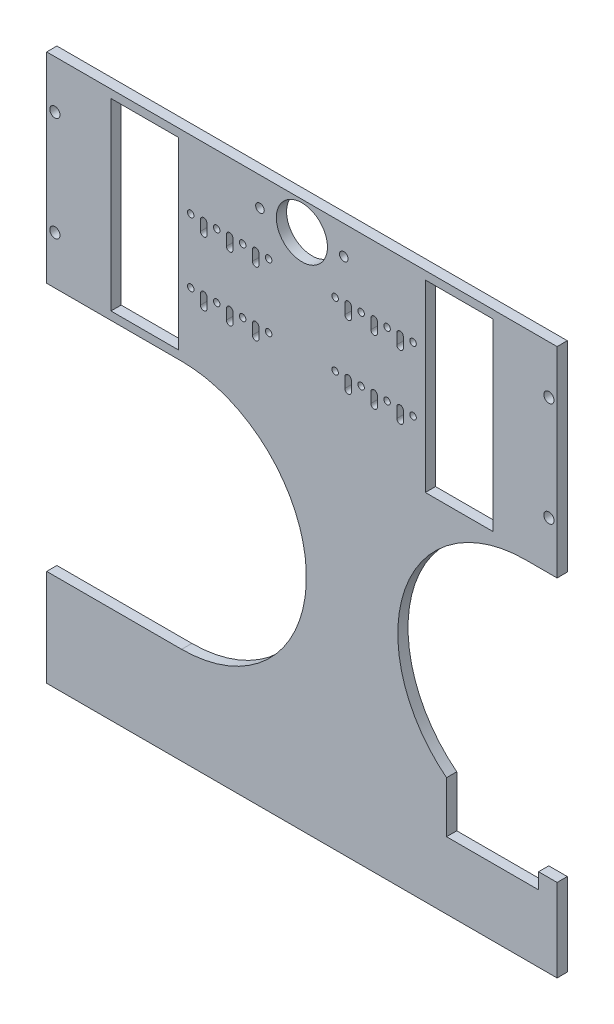
SolidWorks part; units mm, degrees
ref_plane "Front Plane" through (0, 0, 0) normal (0, 0, 1) x (1, 0, 0)
ref_plane "Top Plane" through (0, 0, 0) normal (0, 1, 0) x (1, 0, 0)
ref_plane "Right Plane" through (0, 0, 0) normal (1, 0, 0) x (0, 0, -1)
sketch "Sketch1" plane through (0, 0, 0) normal (0, 0, 1) x (1, 0, 0)
  line L0 (124.8, 0) -> (124.8, -350.4) construction
  line L1 (0, 0) -> (249.6, 0)
  line L2 (0, 0) -> (0, -350.4)
  line L3 (0, -350.4) -> (249.6, -350.4)
  line L4 (249.6, 0) -> (249.6, -350.4)
  line L9 (185.16, -4) -> (218.16, -4)
  line L10 (185.16, -4) -> (185.16, -94)
  line L11 (185.16, -94) -> (218.16, -94)
  line L12 (218.16, -4) -> (218.16, -94)
  line L13 (179.16, -49) -> (228.95, -49) construction
  line L14 (141.06, -33.375) -> (147.41, -33.375) construction
  line L15 (145.3, -14) -> (104.3, -14) construction
  line L21 (179.16, -49) -> (218.16, -49) construction
  line L25 (141.06, -64.625) -> (147.41, -64.625) construction
  line L32 (147.41, -33.375) -> (147.41, -38.375) construction
  line L33 (145.8225, -33.375) -> (145.8225, -38.375)
  line L34 (148.9975, -33.375) -> (148.9975, -38.375)
  line L35 (160.11, -33.375) -> (160.11, -38.375) construction
  line L36 (158.52, -33.375) -> (158.52, -38.375)
  line L37 (161.7, -33.375) -> (161.7, -38.375)
  line L38 (172.81, -33.375) -> (172.81, -38.375) construction
  line L39 (171.22, -33.375) -> (171.22, -38.375)
  line L40 (174.4, -33.375) -> (174.4, -38.375)
  line L41 (147.41, -33.375) -> (153.76, -33.375) construction
  line L42 (153.76, -33.375) -> (160.11, -33.375) construction
  line L43 (160.11, -33.375) -> (166.46, -33.375) construction
  line L44 (166.46, -33.375) -> (172.81, -33.375) construction
  line L45 (172.81, -33.375) -> (179.16, -33.375) construction
  line L48 (228.95, -49) -> (147.41, -49) construction
  line L52 (204.16, -4) -> (204.16, -94) construction
  line L53 (194.16, -4) -> (214.16, -4) construction
  line L54 (194.16, -4) -> (194.16, -94) construction
  line L55 (194.16, -94) -> (214.16, -94) construction
  line L56 (214.16, -4) -> (214.16, -94) construction
  line L62 (147.41, -64.625) -> (147.41, -69.625) construction
  line L65 (145.8225, -64.625) -> (145.8225, -69.625)
  line L68 (148.9975, -64.625) -> (148.9975, -69.625)
  line L71 (160.11, -64.625) -> (160.11, -69.625) construction
  line L78 (158.52, -64.625) -> (158.52, -69.625)
  line L79 (161.7, -64.625) -> (161.7, -69.625)
  line L80 (172.81, -64.625) -> (172.81, -69.625) construction
  line L83 (171.22, -64.625) -> (171.22, -69.625)
  line L87 (147.41, -49) -> (102.19, -49) construction
  line L90 (179.16, -33.375) -> (179.16, -64.625) construction
  line L93 (147.41, -33.375) -> (147.41, -49) construction
  line L102 (245.6, -23.5) -> (245.6, -74.5) construction
  line L103 (218.16, -49) -> (245.6, -49) construction
  line L105 (174.4, -64.625) -> (174.4, -69.625)
  line L106 (147.41, -64.625) -> (153.76, -64.625) construction
  line L107 (153.76, -64.625) -> (160.11, -64.625) construction
  line L108 (160.11, -64.625) -> (166.46, -64.625) construction
  line L109 (166.46, -64.625) -> (172.81, -64.625) construction
  line L110 (172.81, -64.625) -> (179.16, -64.625) construction
  line L111 (102.19, -33.375) -> (102.19, -38.375) construction
  line L112 (103.7775, -33.375) -> (103.7775, -38.375)
  line L113 (100.6025, -33.375) -> (100.6025, -38.375)
  line L114 (89.49, -33.375) -> (89.49, -38.375) construction
  line L115 (91.08, -33.375) -> (91.08, -38.375)
  line L116 (87.9, -33.375) -> (87.9, -38.375)
  line L117 (76.79, -33.375) -> (76.79, -38.375) construction
  line L118 (78.38, -33.375) -> (78.38, -38.375)
  line L119 (75.2, -33.375) -> (75.2, -38.375)
  line L120 (102.19, -64.625) -> (102.19, -69.625) construction
  line L121 (103.7775, -64.625) -> (103.7775, -69.625)
  line L122 (100.6025, -64.625) -> (100.6025, -69.625)
  line L123 (89.49, -64.625) -> (89.49, -69.625) construction
  line L124 (91.08, -64.625) -> (91.08, -69.625)
  line L125 (87.9, -64.625) -> (87.9, -69.625)
  line L126 (76.79, -64.625) -> (76.79, -69.625) construction
  line L127 (78.38, -64.625) -> (78.38, -69.625)
  line L128 (75.2, -64.625) -> (75.2, -69.625)
  line L129 (76.79, -64.625) -> (70.44, -64.625) construction
  line L130 (83.14, -64.625) -> (76.79, -64.625) construction
  line L131 (89.49, -64.625) -> (83.14, -64.625) construction
  line L132 (95.84, -64.625) -> (89.49, -64.625) construction
  line L133 (102.19, -64.625) -> (95.84, -64.625) construction
  line L134 (31.44, -49) -> (4, -49) construction
  line L135 (4, -23.5) -> (4, -74.5) construction
  line L136 (102.19, -33.375) -> (102.19, -49) construction
  line L137 (70.44, -33.375) -> (70.44, -64.625) construction
  line L139 (35.44, -4) -> (35.44, -94) construction
  line L140 (55.44, -94) -> (35.44, -94) construction
  line L141 (55.44, -4) -> (55.44, -94) construction
  line L142 (55.44, -4) -> (35.44, -4) construction
  line L143 (45.44, -4) -> (45.44, -94) construction
  line L144 (20.65, -49) -> (102.19, -49) construction
  line L145 (76.79, -33.375) -> (70.44, -33.375) construction
  line L146 (83.14, -33.375) -> (76.79, -33.375) construction
  line L147 (89.49, -33.375) -> (83.14, -33.375) construction
  line L148 (95.84, -33.375) -> (89.49, -33.375) construction
  line L149 (102.19, -33.375) -> (95.84, -33.375) construction
  line L150 (108.54, -64.625) -> (102.19, -64.625) construction
  line L151 (70.44, -49) -> (31.44, -49) construction
  line L152 (108.54, -33.375) -> (102.19, -33.375) construction
  line L153 (70.44, -49) -> (20.65, -49) construction
  line L154 (31.44, -4) -> (31.44, -94)
  line L155 (64.44, -94) -> (31.44, -94)
  line L156 (64.44, -4) -> (64.44, -94)
  line L157 (64.44, -4) -> (31.44, -4)
  arc A6 (174.4, -33.375) -> (171.22, -33.375) centre (172.81, -33.375) cw construction
  arc A7 (171.22, -33.375) -> (174.4, -33.375) centre (172.81, -33.375) cw
  arc A10 (158.52, -33.375) -> (161.7, -33.375) centre (160.11, -33.375) cw
  arc A11 (161.7, -33.375) -> (158.52, -33.375) centre (160.11, -33.375) cw construction
  arc A14 (145.8225, -33.375) -> (148.9975, -33.375) centre (147.41, -33.375) cw
  arc A15 (148.9975, -33.375) -> (145.8225, -33.375) centre (147.41, -33.375) cw construction
  circle A38 centre (104.3, -14) radius 2.1
  arc A39 (148.9975, -38.375) -> (145.8225, -38.375) centre (147.41, -38.375) cw
  arc A41 (161.7, -38.375) -> (158.52, -38.375) centre (160.11, -38.375) cw
  arc A43 (174.4, -38.375) -> (171.22, -38.375) centre (172.81, -38.375) cw
  circle A84 centre (245.6, -23.5) radius 2.5
  circle A85 centre (245.6, -74.5) radius 2.5
  circle A109 centre (145.3, -14) radius 2.1
  circle A179 centre (179.16, -33.375) radius 1.59
  arc A182 (174.4, -64.625) -> (171.22, -64.625) centre (172.81, -64.625) cw construction
  arc A183 (171.22, -64.625) -> (174.4, -64.625) centre (172.81, -64.625) cw
  arc A184 (158.52, -64.625) -> (161.7, -64.625) centre (160.11, -64.625) cw
  arc A185 (161.7, -64.625) -> (158.52, -64.625) centre (160.11, -64.625) cw construction
  arc A188 (145.8225, -64.625) -> (148.9975, -64.625) centre (147.41, -64.625) cw
  arc A189 (148.9975, -64.625) -> (145.8225, -64.625) centre (147.41, -64.625) cw construction
  arc A193 (148.9975, -69.625) -> (145.8225, -69.625) centre (147.41, -69.625) cw
  arc A195 (161.7, -69.625) -> (158.52, -69.625) centre (160.11, -69.625) cw
  arc A197 (174.4, -69.625) -> (171.22, -69.625) centre (172.81, -69.625) cw
  circle A198 centre (179.16, -64.625) radius 1.59
  circle A199 centre (124.8, -14) radius 12.5
  circle A200 centre (141.06, -33.375) radius 1.59
  circle A201 centre (153.76, -33.375) radius 1.59
  circle A202 centre (166.46, -33.375) radius 1.59
  circle A203 centre (141.06, -64.625) radius 1.59
  circle A204 centre (153.76, -64.625) radius 1.59
  circle A205 centre (166.46, -64.625) radius 1.59
  arc A206 (103.7775, -33.375) -> (100.6025, -33.375) centre (102.19, -33.375) ccw
  arc A207 (100.6025, -38.375) -> (103.7775, -38.375) centre (102.19, -38.375) ccw
  arc A208 (91.08, -33.375) -> (87.9, -33.375) centre (89.49, -33.375) ccw
  arc A209 (87.9, -38.375) -> (91.08, -38.375) centre (89.49, -38.375) ccw
  arc A210 (78.38, -33.375) -> (75.2, -33.375) centre (76.79, -33.375) ccw
  arc A211 (75.2, -38.375) -> (78.38, -38.375) centre (76.79, -38.375) ccw
  arc A212 (103.7775, -64.625) -> (100.6025, -64.625) centre (102.19, -64.625) ccw
  arc A213 (100.6025, -69.625) -> (103.7775, -69.625) centre (102.19, -69.625) ccw
  arc A214 (91.08, -64.625) -> (87.9, -64.625) centre (89.49, -64.625) ccw
  arc A215 (87.9, -69.625) -> (91.08, -69.625) centre (89.49, -69.625) ccw
  arc A216 (78.38, -64.625) -> (75.2, -64.625) centre (76.79, -64.625) ccw
  arc A217 (75.2, -69.625) -> (78.38, -69.625) centre (76.79, -69.625) ccw
  arc A218 (100.6025, -64.625) -> (103.7775, -64.625) centre (102.19, -64.625) ccw construction
  arc A219 (87.9, -64.625) -> (91.08, -64.625) centre (89.49, -64.625) ccw construction
  arc A220 (75.2, -64.625) -> (78.38, -64.625) centre (76.79, -64.625) ccw construction
  arc A221 (100.6025, -33.375) -> (103.7775, -33.375) centre (102.19, -33.375) ccw construction
  arc A222 (87.9, -33.375) -> (91.08, -33.375) centre (89.49, -33.375) ccw construction
  arc A223 (75.2, -33.375) -> (78.38, -33.375) centre (76.79, -33.375) ccw construction
  circle A224 centre (83.14, -64.625) radius 1.59
  circle A225 centre (95.84, -64.625) radius 1.59
  circle A226 centre (108.54, -64.625) radius 1.59
  circle A227 centre (83.14, -33.375) radius 1.59
  circle A228 centre (95.84, -33.375) radius 1.59
  circle A229 centre (108.54, -33.375) radius 1.59
  circle A230 centre (70.44, -64.625) radius 1.59
  circle A234 centre (70.44, -33.375) radius 1.59
  circle A236 centre (4, -74.5) radius 2.5
  circle A237 centre (4, -23.5) radius 2.5
  point P64 (147.41, -49)
  point P65 (102.19, -35.875)
  point P69 (228.95, -49)
  point P71 (221, -87.34)
  point P76 (233.7, -87.34)
  point P78 (221, -54.5)
  point P82 (233.7, -54.5)
  point P86 (246.4, -54.5)
  point P93 (179.16, -49)
  point P97 (246.4, -87.34)
  point P104 (89.49, -35.875)
  point P111 (76.79, -35.875)
  point P119 (102.19, -67.125)
  point P126 (89.49, -67.125)
  point P133 (76.79, -67.125)
  point P155 (124.8, -76.5574)
  point P166 (124.8, -49)
  point P183 (124.8, -76.5574)
  point P199 (70.44, -49)
  point P200 (20.65, -49)
  point P201 (102.19, -49)
  dimension "D5" = 20
  dimension "D10" = 5
  dimension "D12" = 3.18
  dimension "D15" = 5
  dimension "D16" = 5
  dimension "D19" = 3.18
  dimension "D20" = 1.5875
  dimension "D21" = 3.18
  dimension "D22" = 1.59
  dimension "D23" = 3.18
  dimension "D24" = 1.59
  dimension "D25" = 3.18
  dimension "D33" = 3.18
  dimension "D34" = 5
  dimension "D35" = 4.2
  dimension "D32" = 1.5875
  dimension "D36" = 1.59
  dimension "D37" = 3.18
  dimension "D39" = 1.59
  dimension "D47" = 3.18
  dimension "D49" = 25
  dimension "D51" = 4.2
  dimension "D1" = 249.6
  dimension "D2" = 350.4
  dimension "D3" = 4
  dimension "D4" = 90
  dimension "D6" = 90
  dimension "D7" = 9
  dimension "D8" = 6
  dimension "D9" = 5
  dimension "D11" = 6.35
  dimension "D13" = 6.35
  dimension "D14" = 89.36
  dimension "D17" = 25.5
  dimension "D18" = 4
  dimension "D26" = 5
  dimension "D27" = 6.35
  dimension "D28" = 6.35
  dimension "D29" = 6.35
  dimension "D30" = 6.35
  dimension "D31" = 6.35
  dimension "D38" = 4
  dimension "D40" = 5
  dimension "D41" = 6.35
  dimension "D42" = 6.35
  dimension "D43" = 6.35
  dimension "D44" = 6.35
  dimension "D45" = 6.35
  dimension "D46" = 5
  dimension "D48" = 31.25
  dimension "D50" = 20.5
  dimension "14" = 14
extrude "Boss-Extrude1" add sketch "Sketch1" along normal blind 5
sketch "Sketch11" plane through (0, 0, 5) normal (0, 0, 1) x (1, 0, 0)
  line L0 (0, -94) -> (249.6, -94) construction
  line L1 (0, 0) -> (0, -350.4) construction
  line L2 (249.6, -350.4) -> (249.6, 0) construction
  line L3 (31.44, -94) -> (64.44, -94) construction
  line L4 (0, -98) -> (249.6, -98) construction
  line L5 (127, -98) -> (127, -350.4) construction
  line L6 (0, -350.4) -> (249.6, -350.4) construction
  line L7 (124.8, -98) -> (124.8, -350.4) construction
  line L8 (249.6, 0) -> (0, 0) construction
  line L9 (0, -3) -> (249.6, -3) construction
  line L10 (244.6, 0) -> (244.6, -350.4) construction
  line L11 (5, 0) -> (5, -350.4) construction
  line L12 (0, -351.918) -> (249.6, -351.918) construction
  line L13 (66, -220) -> (0, -220)
  line L14 (66, -98) -> (0, -98)
  line L16 (234.206, -98) -> (249.6, -98)
  line L17 (0, -98) -> (0, -220)
  line L18 (249.6, -98) -> (249.6, -226.9273)
  line L19 (0, -124) -> (249.6, -124) construction
  line L20 (126, -98) -> (126, -350.4) construction
  line L21 (-27.2864, 0) -> (507.3192, -350.4) construction
  line L22 (191.6195, 0) -> (726.2251, -350.4) construction
  line L23 (0, -121.5) -> (249.6, -121.5) construction
  line L24 (0, -98) -> (110.797, -200.4033) construction
  line L25 (195.5325, -234.598) -> (195.5325, -209.598)
  line L26 (195.5325, -234.598) -> (240.5325, -234.598)
  line L27 (161.7, -38.375) -> (161.7, -33.375) construction
  line L28 (249.6, -226.9273) -> (240.5325, -226.9273)
  line L29 (240.5325, -226.9273) -> (240.5325, -234.598)
  line L30 (75.2, -33.375) -> (75.2, -38.375) construction
  arc A0 (66, -220) -> (66, -98) centre (66, -159) ccw
  arc A1 (234.206, -98) -> (195.5325, -209.598) centre (234.206, -160.5) ccw
  circle A2 centre (66, -64) radius 61 construction
  circle A3 centre (182.1, -65.5) radius 62.5 construction
  circle A4 centre (66, -64) radius 60 construction
  circle A5 centre (182.1, -65.5) radius 60 construction
  circle A6 centre (-9.0472, -24.71) radius 24.71 construction
  circle A7 centre (150.71, -146.21) radius 24.71 construction
  circle A8 centre (66, -159) radius 60 construction
  circle A9 centre (234.206, -160.5) radius 60 construction
  circle A10 centre (256.3426, -24.71) radius 24.71 construction
  point P65 (0, 0)
  point P66 (249.6, -225.3019)
  point P67 (249.6, -229.1925)
  point P68 (0, 0)
  point P69 (240.3363, -227.9273)
  point P70 (235.6189, -164.5)
  point P74 (201.0494, -216.5692)
  point P77 (0, 0)
  dimension "D1" = 122
  dimension "D4" = 125
  dimension "D5" = 122
  dimension "D3" = 125
  dimension "D9" = 120
  dimension "D10" = 120
  dimension "D11" = 120
  dimension "D12" = 49.42
  dimension "D13" = 49.42
  dimension "D14" = 120
  dimension "D16" = 49.42
  dimension "D2" = 4
  dimension "D6" = 3
  dimension "D7" = 5
  dimension "D8" = 5
  dimension "D15" = 2.5
  dimension "D17" = 45
  dimension "D18" = 25
extrude "Cut-Extrude1" cut sketch "Sketch11" against normal through all
sketch "Sketch12" plane through (0, -350.4, 0) normal (0, -1, 0) x (1, 0, 0)
  line L0 (0, 0) -> (249.6, 0)
  line L1 (0, 0) -> (0, 5)
  line L2 (249.6, 0) -> (249.6, 5)
  line L3 (0, 5) -> (249.6, 5)
  line L4 (0, 5) -> (249.6, 5) construction
extrude "Cut-Extrude2" cut sketch "Sketch12" against normal blind 83
